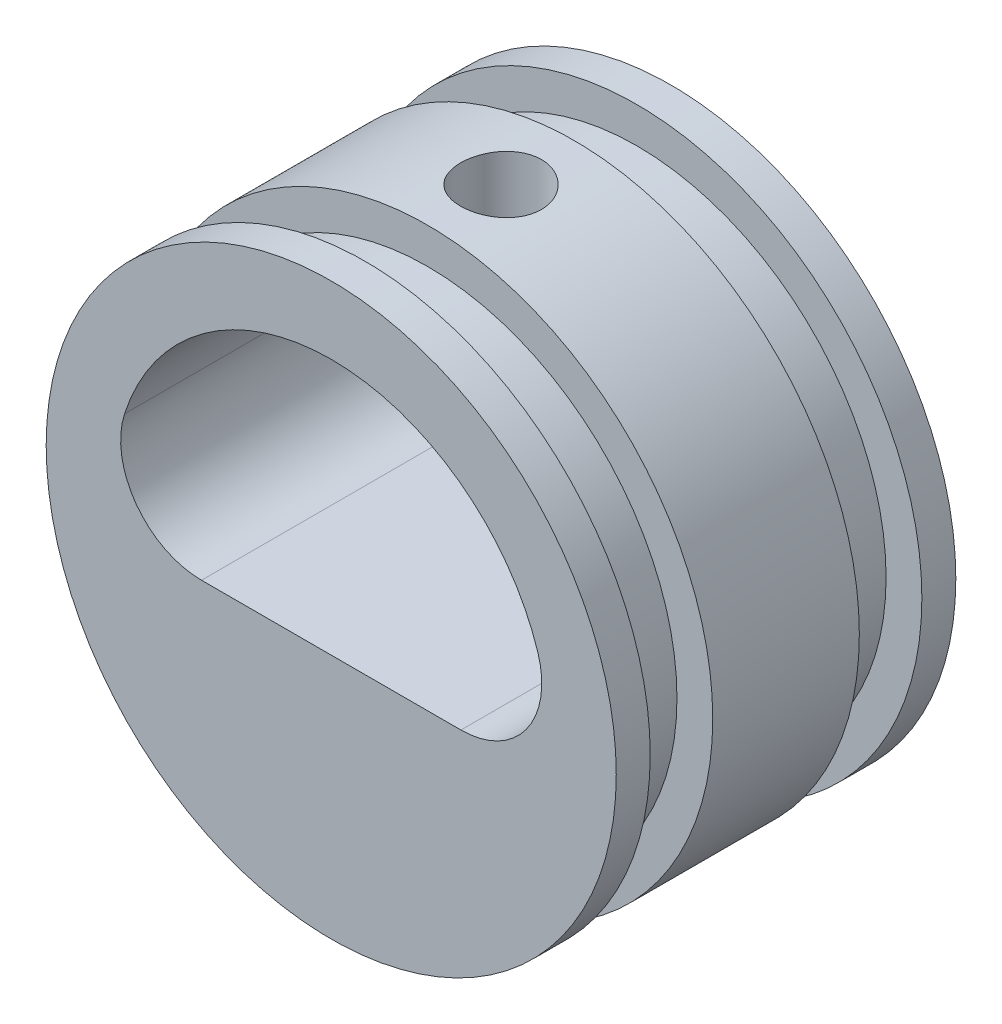
SolidWorks part; units mm, degrees
ref_plane "Front Plane" through (0, 0, 0) normal (0, 0, 1) x (1, 0, 0)
ref_plane "Top Plane" through (0, 0, 0) normal (0, 1, 0) x (1, 0, 0)
ref_plane "Right Plane" through (0, 0, 0) normal (1, 0, 0) x (0, 0, -1)
sketch "Sketch1" plane through (0, 0, 0) normal (0, 0, 1) x (1, 0, 0)
  circle A0 centre (0, 0) radius 16.7894
  dimension "D1" = 33.5788
extrude "Boss-Extrude1" add sketch "Sketch1" along normal blind 20
sketch "Sketch2" plane through (0, 0, 0) normal (1, 0, 0) x (0, 0, -1)
  line L0 (0, 16.7894) -> (-20, 16.7894) construction
  line L1 (-18, 16.7894) -> (-14.317, 16.7894)
  line L2 (-18, 16.7894) -> (-18, 14.6812)
  line L3 (-18, 14.6812) -> (-14.317, 14.6812)
  line L4 (-14.317, 16.7894) -> (-14.317, 14.6812)
  line L5 (-21.2407, 0) -> (1.9138, 0) construction
  line L6 (-20, 16.7894) -> (-20, -16.7894) construction
  line L7 (0, -16.7894) -> (0, 16.7894) construction
  line L8 (-2, 16.7894) -> (-5.683, 16.7894)
  line L9 (-2, 16.7894) -> (-2, 14.6812)
  line L10 (-2, 14.6812) -> (-5.683, 14.6812)
  line L11 (-5.683, 16.7894) -> (-5.683, 14.6812)
  dimension "D1" = 3.683
  dimension "D2" = 2.1082
  dimension "D3" = 2
  dimension "D4" = 2
revolve "Cut-Revolve1" cut sketch "Sketch2" angle 360 about L5
sketch "Sketch3" plane through (0, 0, 20) normal (0, 0, 1) x (1, 0, 0)
  line L0 (-12.5809, -2.3) -> (12.5809, -2.3)
  line L1 (-18.2206, 0) -> (27.3408, 0) construction
  arc A0 (12.5809, -2.3) -> (-12.5809, -2.3) centre (0, 0) ccw
  circle A1 centre (0, 0) radius 16.7894 construction
  dimension "D1" = 4
  dimension "D2" = 2.3
extrude "Cut-Extrude1" cut sketch "Sketch3" against normal through all
ref_point "Point1"
fillet "Fillet1" radius 4.7625 2 edges at (12.5809, -2.3, 10) (-12.5809, -2.3, 10)
ref_plane "Plane1" through (0, 16.7894, 0) normal (0, 1, 0) x (-1, 0, 0)
hole_wizard "3/16 (0.1875) Diameter Hole1" positions "Sketch6" profile "Sketch5" hole size "3/16" standard "Ansi Inch"
sketch "Sketch6" plane through (0, 16.7894, 0) normal (0, 1, 0) x (-1, 0, 0)
  line L3 (0, -3.916) -> (0, 34.5317) construction
  line L6 (16.7894, 20) -> (-16.7894, 20) construction
  line L7 (-16.7894, 0) -> (16.7894, 0) construction
  circle A0 centre (0, 10) radius 10 construction
  point P1 (0, 10)
sketch "Sketch5" plane through (0, 16.7894, 10) normal (1, 0, 0) x (0, 0, 1)
  line L0 (0, 0) -> (0, 12.9745)
  line L1 (0, 12.9745) -> (2.3812, 11.5437)
  line L2 (2.3812, 11.5437) -> (2.3813, 0)
  line L5 (2.3813, 0) -> (0, 0)
  line L10 (0, 12.9745) -> (-2.3813, 11.5437) construction
  line L11 (0, -6.35) -> (0, 107.95) construction
  dimension "Hole Dia." = 4.7625
  dimension "Hole Depth" = 11.5437
  dimension "Drill Angle" = 118
